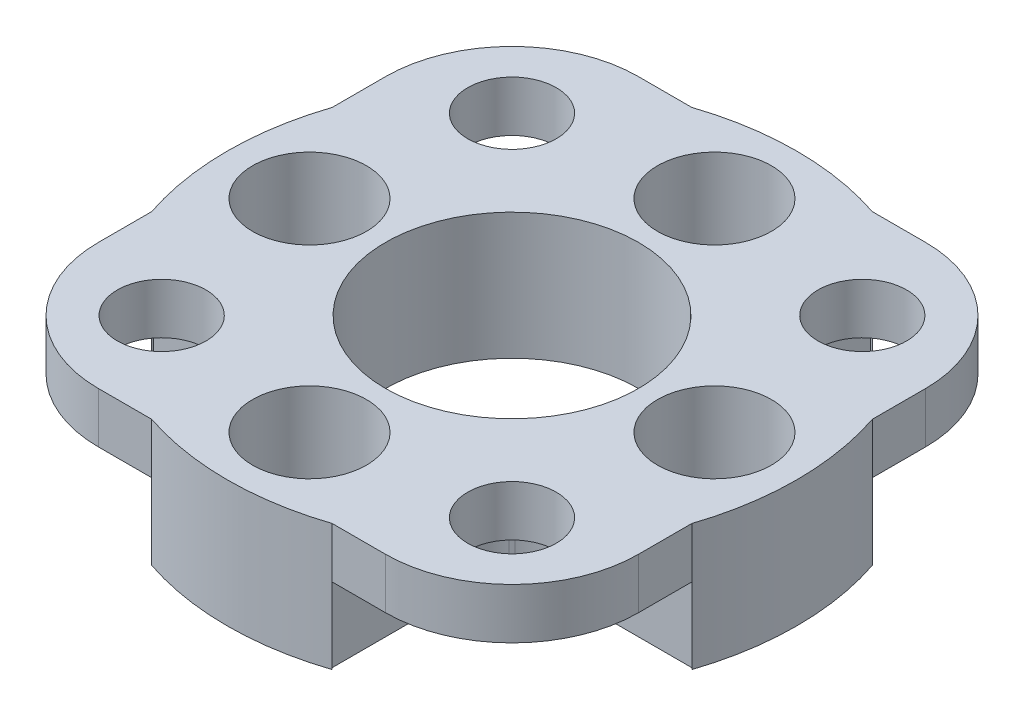
SolidWorks part; units mm, degrees
ref_plane "Plan de face" through (0, 0, 0) normal (0, 0, 1) x (1, 0, 0)
ref_plane "Plan de dessus" through (0, 0, 0) normal (0, 1, 0) x (1, 0, 0)
ref_plane "Plan de droite" through (0, 0, 0) normal (1, 0, 0) x (0, 0, -1)
sketch "Esquisse1" plane through (0, 0, 0) normal (0, 1, 0) x (1, 0, 0)
  circle A0 centre (0, 0) radius 11.25
  point P1 (5.7087, 9.5)
  dimension "D1" = 22.5
extrude "Boss.-Extru.1" add sketch "Esquisse1" along normal blind 2
sketch "Esquisse8" plane through (0, 0, 0) normal (0, -1, 0) x (1, 0, 0)
  circle A0 centre (0, 0) radius 11.25
  circle A1 centre (0, 0) radius 11.25 construction
  point P1 (6.026, -9.5)
  point P5 (-6.3359, -10.5372)
  point P8 (0, 0)
extrude "Boss.-Extru.2" add sketch "Esquisse8" along normal blind 3
sketch "Esquisse15" plane through (0, 2, 0) normal (0, 1, 0) x (1, 0, 0)
  line L1 (-10.67, 10.67) -> (10.67, 10.67)
  line L2 (-10.67, 10.67) -> (-10.67, -10.67)
  line L3 (-10.67, -10.67) -> (10.67, -10.67)
  line L4 (10.67, 10.67) -> (10.67, -10.67)
  point P4 (0, 10.67)
  point P6 (10.67, 0)
  dimension "D1" = 21.34
extrude "Boss.-Extru.3" add sketch "Esquisse15" against normal blind 2
sketch "Esquisse14" plane through (0, -3, 0) normal (0, -1, 0) x (1, 0, 0)
  circle A0 centre (0, 0) radius 5
  dimension "D1" = 10
extrude "Enlèv. mat.-Extru.3" cut sketch "Esquisse14" against normal blind 6
hole_wizard "Dégagement M21" positions "Esquisse16" profile "Esquisse17" size "M2" standard "Ansi Metric" slot yes end condition through all
sketch "Esquisse16" plane through (0, 2, 0) normal (0, 1, 0) x (1, 0, 0)
  line L0 (10.67, -10.67) -> (10.67, -3.5656) construction
  line L1 (3.5656, -10.67) -> (10.67, -10.67) construction
  line L2 (-3.5656, 10.67) -> (-10.67, 10.67) construction
  line L3 (-10.67, 10.67) -> (-10.67, 3.5656) construction
  point P0 (6.92, -6.92)
  point P2 (-6.92, -6.92)
  point P4 (-6.92, 6.92)
  point P6 (6.92, 6.92)
  point P13 (0, 0)
  point P14 (0, 0)
  point P15 (0, 0)
  point P16 (0, 0)
  point P21 (0, 0)
  point P22 (0, 0)
  dimension "D1" = 3.75
  dimension "D2" = 3.75
  dimension "D3" = 3.75
  dimension "D4" = 3.75
sketch "Esquisse17" plane through (6.92, 2, 6.92) normal (1, 0, 0) x (0, 0, 1)
  line L0 (0, 0) -> (0, 5)
  line L1 (0, 5) -> (1.75, 5)
  line L2 (1.75, 5) -> (1.75, 0)
  line L5 (1.75, 0) -> (0, 0)
  line L11 (0, -6.35) -> (0, 107.95) construction
  dimension "Diamètre du perçage jusqu'au prochain" = 3.5
  dimension "Profondeur du perçage jusqu'au prochain" = 5
sketch "Esquisse18" plane through (0, 0, 0) normal (0, -1, 0) x (1, 0, 0)
  line L0 (-3.5, -10.67) -> (-3.5, -5)
  line L1 (-10.67, 10.67) -> (-3.5, 10.67)
  line L2 (-10.67, 10.67) -> (-10.67, 3.5)
  line L3 (-10.67, 3.5) -> (-5, 3.5)
  line L4 (-3.5, 10.67) -> (-3.5, 5)
  line L5 (10.67, 10.67) -> (3.5, 10.67)
  line L6 (10.67, 10.67) -> (10.67, 3.5)
  line L7 (10.67, 3.5) -> (5, 3.5)
  line L8 (3.5, 10.67) -> (3.5, 5)
  line L9 (10.67, -10.67) -> (3.5, -10.67)
  line L10 (10.67, -10.67) -> (10.67, -3.5)
  line L11 (10.67, -3.5) -> (5, -3.5)
  line L12 (3.5, -10.67) -> (3.5, -5)
  line L13 (-10.67, -10.67) -> (-3.5, -10.67)
  line L14 (-10.67, -10.67) -> (-10.67, -3.5)
  line L15 (-10.67, -3.5) -> (-5, -3.5)
  line L17 (-3.5, 5) -> (3.5, 5)
  line L19 (-3.5, -5) -> (3.5, -5)
  line L22 (5, 3.5) -> (5, -3.5)
  line L24 (-5, 3.5) -> (-5, -3.5)
  circle A2 centre (0, 0) radius 5 construction
  point P8 (0, 0)
  point P13 (-3.1208, -1.3003)
  point P18 (5, 0)
  point P30 (-5, 0)
  point P31 (0, 5)
  point P32 (0, -5)
  point P33 (0, 0)
  dimension "D1" = 7
  dimension "D2" = 7
extrude "Enlèv. mat.-Extru.11" cut sketch "Esquisse18" along normal blind 3
fillet "Congé1" radius 5 4 edges at (-10.67, 1, -10.67) (10.67, 1, -10.67) (10.67, 1, 10.67) (-10.67, 1, 10.67)
sketch "Esquisse20" plane through (0, 0, 0) normal (0, -1, 0) x (1, 0, 0)
  circle A0 centre (0, 0) radius 5
  circle A1 centre (0, 0) radius 6.1033
  arc A2 (5, 0) -> (0, 5) centre (0, 0) ccw construction
extrude "Boss.-Extru.5" add sketch "Esquisse20" along normal blind 3
fillet "Congé3" radius 2.5 8 edges at (-5, -1.5, -3.5) (-3.5, -1.5, -5) (3.5, -1.5, -5) (5, -1.5, -3.5) (5, -1.5, 3.5) (3.5, -1.5, 5) (-3.5, -1.5, 5) (-5, -1.5, 3.5)
hole_wizard "Chambrage pour vis à tête cylindrique à 6 pans creux (ou vis CHC) M21" positions "Esquisse12" profile "Esquisse13" counterbore size "M2" standard "Ansi Metric" end condition through all
sketch "Esquisse12" plane through (0, 2, 0) normal (0, 1, 0) x (1, 0, 0)
  line L0 (-8, 0) -> (0, 0) construction
  line L1 (0, 0) -> (0, -8) construction
  line L3 (0, 0) -> (8, 0) construction
  point P0 (-8, 0)
  point P2 (0, -8)
  point P4 (8, 0)
  point P19 (0, 8)
  point P22 (0, 0)
  dimension "D1" = 8
  dimension "D2" = 8
sketch "Esquisse13" plane through (-8, 2, 0) normal (1, 0, 0) x (0, 0, 1)
  line L0 (0, 0) -> (0, 5)
  line L1 (0, 5) -> (1.25, 5)
  line L3 (1.25, 5) -> (1.25, 3.3)
  line L4 (1.25, 3.3) -> (2.25, 3.3)
  line L5 (2.25, 3.3) -> (2.25, 0)
  line L7 (2.25, 0) -> (0, 0)
  line L11 (0, -6.35) -> (0, 107.95) construction
  dimension "Diamètre du perçage jusqu'au prochain" = 2.5
  dimension "Profondeur du perçage jusqu'au prochain" = 5
  dimension "Diamètre du chambrage" = 4.5
  dimension "Profondeur du chambrage" = 3.3
